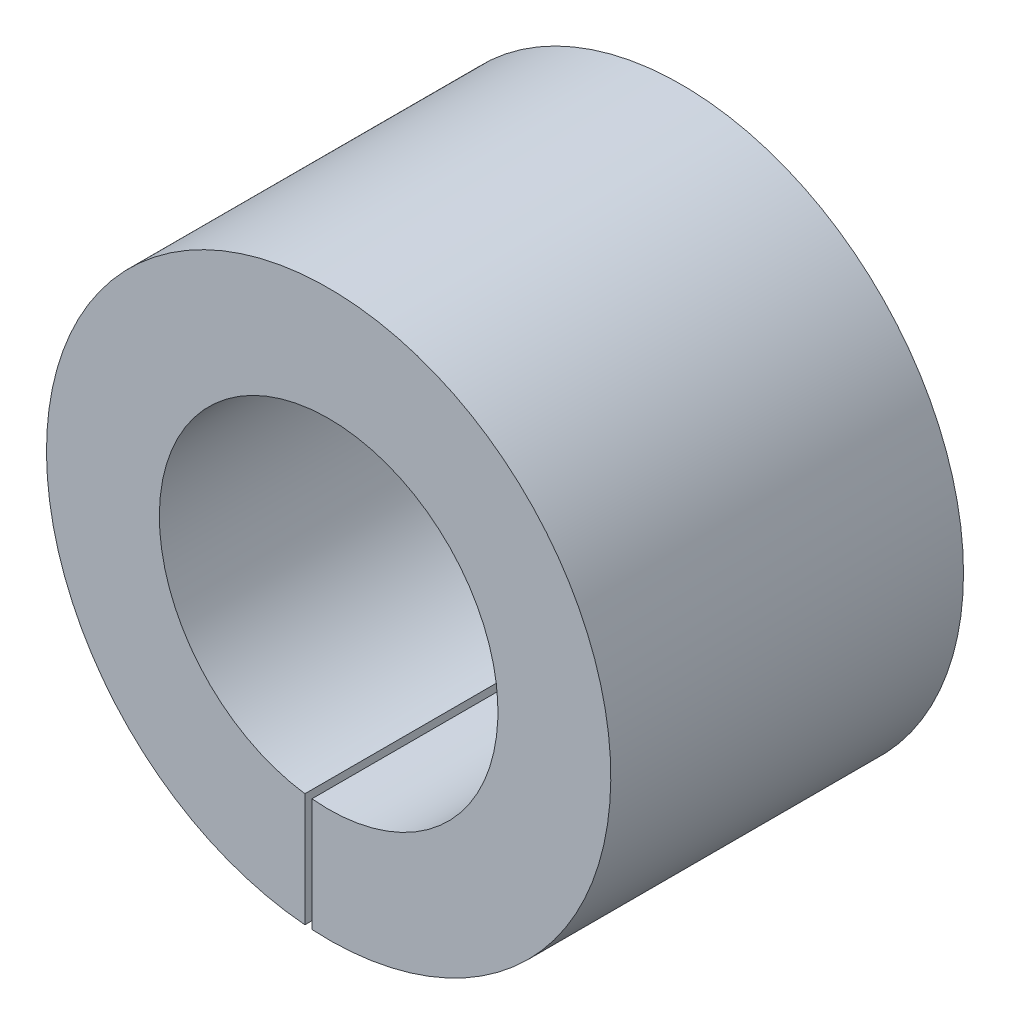
SolidWorks part; units mm, degrees
ref_plane "前视基准面" through (0, 0, 0) normal (0, 0, 1) x (1, 0, 0)
ref_plane "上视基准面" through (0, 0, 0) normal (0, 1, 0) x (1, 0, 0)
ref_plane "右视基准面" through (0, 0, 0) normal (1, 0, 0) x (0, 0, -1)
sketch "草图1" plane through (0, 0, 0) normal (0, 0, 1) x (1, 0, 0)
  circle A0 centre (0, 0) radius 20
  circle A1 centre (0, 0) radius 12
  dimension "D1" = 40
  dimension "D2" = 24
extrude "凸台-拉伸1" add sketch "草图1" along normal blind 25
sketch "草图2" plane through (0, 0, 25) normal (0, 0, 1) x (1, 0, 0)
  line L1 (-1.6846, -2.2632) -> (-1.1846, -2.2632)
  line L2 (-1.6846, -2.2632) -> (-1.6846, -21.5647)
  line L3 (-1.6846, -21.5647) -> (-1.1846, -21.5647)
  line L4 (-1.1846, -2.2632) -> (-1.1846, -21.5647)
  line L5 (-1.6846, -2.2632) -> (-1.1846, -21.5647) construction
  line L6 (-1.6846, -21.5647) -> (-1.1846, -2.2632) construction
  circle A0 centre (0, 0) radius 12 construction
  point P0 (-1.4346, -11.9139)
  dimension "D1" = 0.5
extrude "切除-拉伸1" cut sketch "草图2" against normal blind 15
sketch "草图3" plane through (0, 0, 0) normal (0, 0, -1) x (-1, 0, 0)
  line L1 (-0.9197, -2.6864) -> (-0.4197, -2.6864)
  line L2 (-0.9197, -2.6864) -> (-0.9197, 18.127)
  line L3 (-0.9197, 18.127) -> (-0.4197, 18.127)
  line L4 (-0.4197, -2.6864) -> (-0.4197, 18.127)
  line L5 (-0.9197, -2.6864) -> (-0.4197, 18.127) construction
  line L6 (-0.9197, 18.127) -> (-0.4197, -2.6864) construction
  point P0 (-0.6697, 7.7203)
  dimension "D1" = 0.5
extrude "切除-拉伸2" cut sketch "草图3" against normal blind 15
